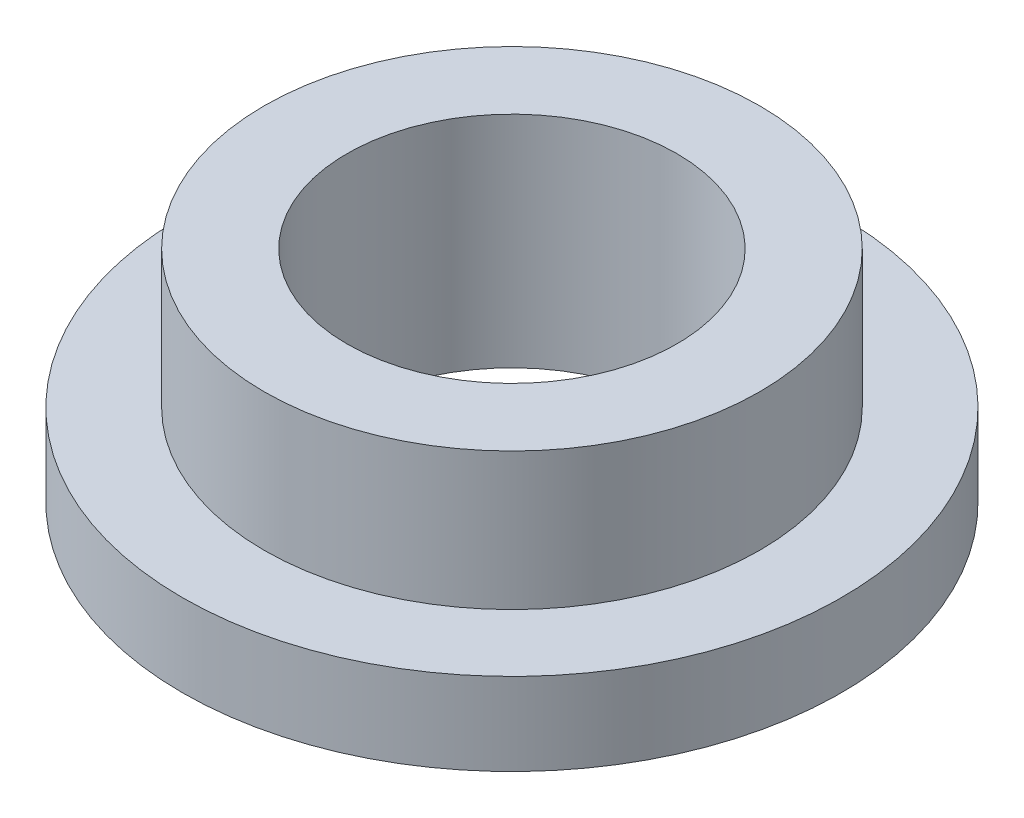
SolidWorks part; units mm, degrees
ref_plane "Front" through (0, 0, 0) normal (0, 0, 1) x (1, 0, 0)
ref_plane "Top" through (0, 0, 0) normal (0, 1, 0) x (1, 0, 0)
ref_plane "Right" through (0, 0, 0) normal (1, 0, 0) x (0, 0, -1)
sketch "Sketch1" plane through (0, 0, 0) normal (0, 1, 0) x (1, 0, 0)
  circle A0 centre (0, 0) radius 6.005
  circle A1 centre (0, 0) radius 9.02
  circle A2 centre (0, 0) radius 12
  dimension "ID" = 12.01
  dimension "OD" = 18.04
  dimension "FlangeOD" = 24
sketch "Sketch2" plane through (0, 0, 0) normal (0, 1, 0) x (1, 0, 0)
  circle A0 centre (0, 0) radius 6.005 construction
  circle A1 centre (0, 0) radius 9.02 construction
  circle A2 centre (0, 0) radius 6.005
  circle A3 centre (0, 0) radius 9.02
extrude "Boss-Extrude1" add sketch "Sketch2" along normal blind 8
sketch "Sketch3" plane through (0, 0, 0) normal (0, 1, 0) x (1, 0, 0)
  circle A0 centre (0, 0) radius 12 construction
  circle A1 centre (0, 0) radius 9.02 construction
  circle A2 centre (0, 0) radius 12
  circle A3 centre (0, 0) radius 9.02
extrude "Boss-Extrude2" add sketch "Sketch3" along normal blind 3
